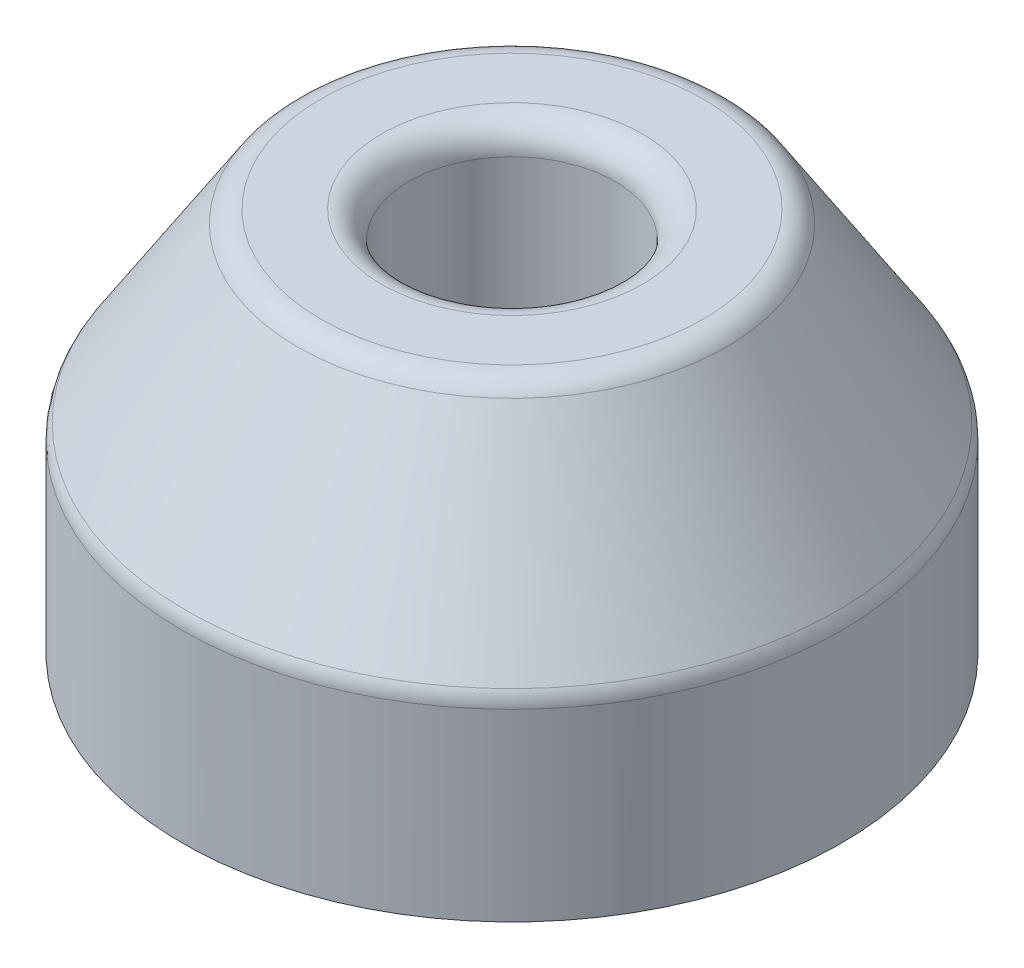
SolidWorks part; units mm, degrees
ref_plane "Piano frontale" through (0, 0, 0) normal (0, 0, 1) x (1, 0, 0)
ref_plane "Piano superiore" through (0, 0, 0) normal (0, 1, 0) x (1, 0, 0)
ref_plane "Piano destro" through (0, 0, 0) normal (1, 0, 0) x (0, 0, -1)
sketch "Schizzo1" plane through (0, 0, 0) normal (0, 0, 1) x (1, 0, 0)
  line L0 (0, -9.9877) -> (0, 37.7761) construction
  line L1 (0, 0) -> (12, 0)
  line L2 (12, 0) -> (12, 7)
  line L3 (12, 7) -> (7.5, 14)
  line L4 (7.5, 14) -> (0, 14)
  line L5 (0, 14) -> (0, 0)
  dimension "D1" = 7.5
  dimension "D2" = 12
  dimension "D3" = 14
  dimension "D4" = 7
revolve "Rivoluzione1" add sketch "Schizzo1" angle 360 about L0
sketch "Schizzo2" plane through (0, 14, 0) normal (0, 1, 0) x (1, 0, 0)
  circle A0 centre (0, 0) radius 3.75
  dimension "D1" = 7.5
extrude "Taglio-Estrusione1" cut sketch "Schizzo2" against normal blind 8
fillet "Fillet1" radius 1 3 edges at (0, 14, 3.75) (0, 14, -7.5) (0, 7, -12)
